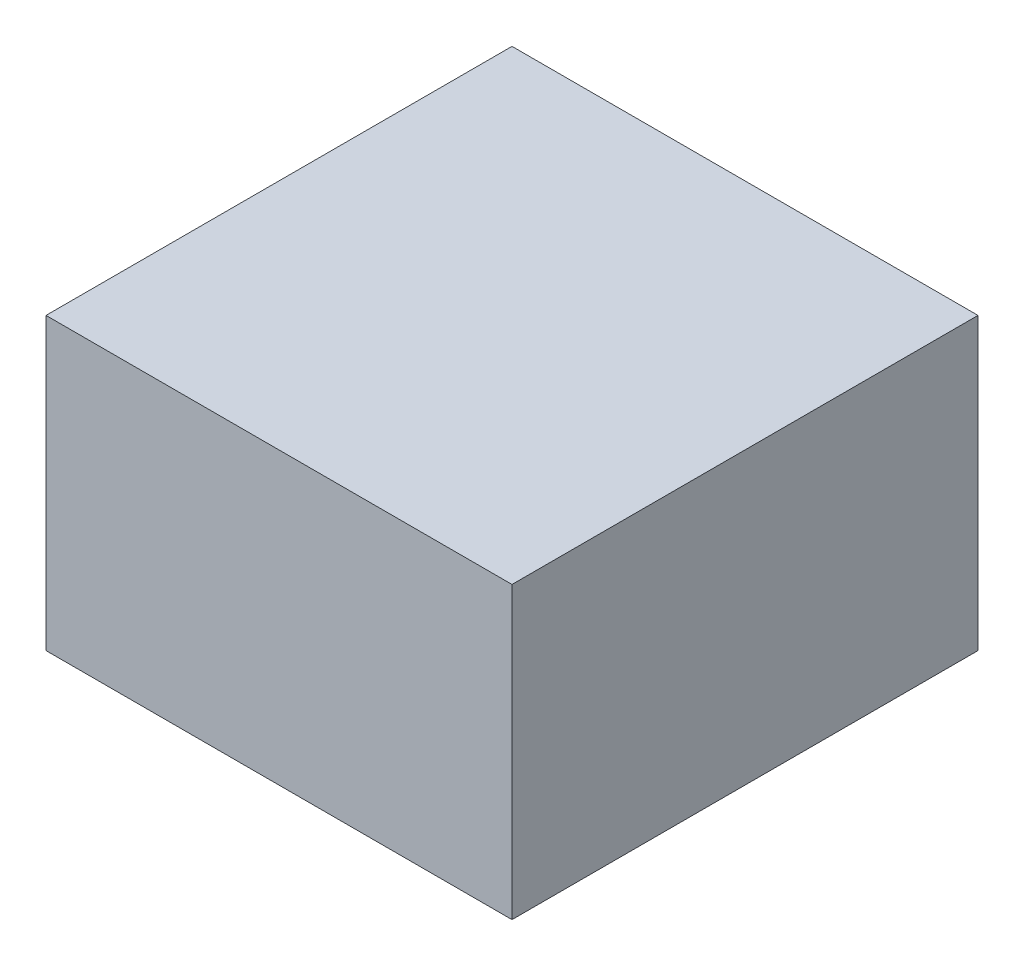
SolidWorks part; units mm, degrees
ref_plane "Front Plane" through (0, 0, 0) normal (0, 0, 1) x (1, 0, 0)
ref_plane "Top Plane" through (0, 0, 0) normal (0, 1, 0) x (1, 0, 0)
ref_plane "Right Plane" through (0, 0, 0) normal (1, 0, 0) x (0, 0, -1)
sketch "Sketch1" plane through (0, 0, 0) normal (0, 1, 0) x (1, 0, 0)
  line L1 (0, 0) -> (154.94, 0)
  line L2 (0, 0) -> (0, -154.94)
  line L3 (0, -154.94) -> (154.94, -154.94)
  line L4 (154.94, 0) -> (154.94, -154.94)
extrude "Boss-Extrude1" add sketch "Sketch1" along normal blind 96.52
